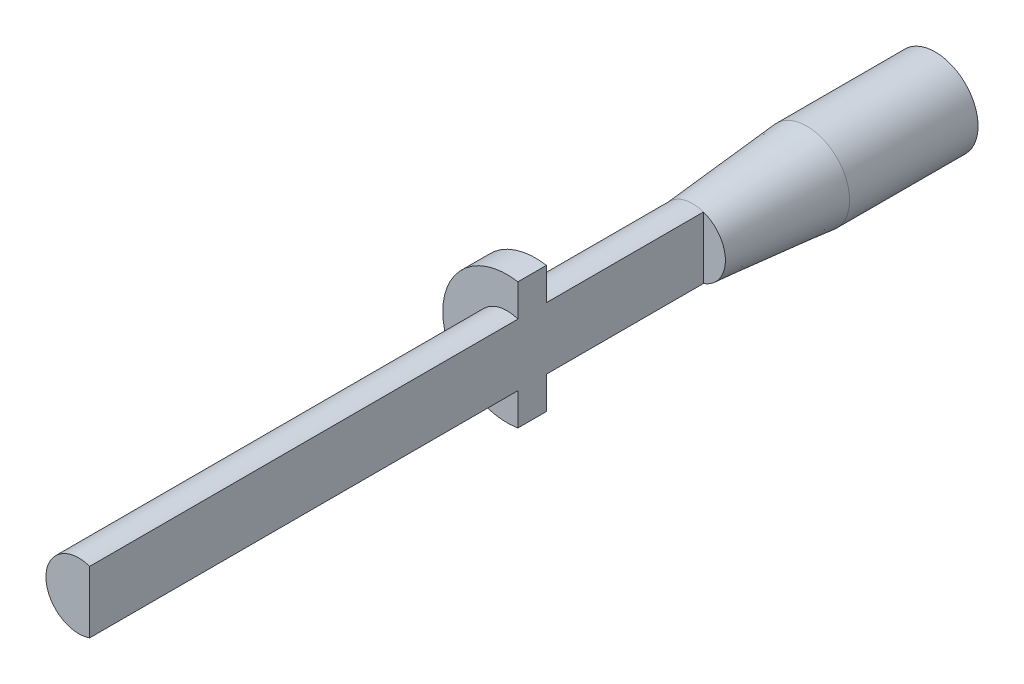
SolidWorks part; units mm, degrees
ref_plane "Front Plane" through (0, 0, 0) normal (0, 0, 1) x (1, 0, 0)
ref_plane "Top Plane" through (0, 0, 0) normal (0, 1, 0) x (1, 0, 0)
ref_plane "Right Plane" through (0, 0, 0) normal (1, 0, 0) x (0, 0, -1)
sketch "Sketch1" plane through (0, 0, 0) normal (0, 0, 1) x (1, 0, 0)
  line L0 (0.7623, -2.17) -> (0.7623, 2.17)
  arc A0 (0.7623, 2.17) -> (0.7623, -2.17) centre (0, 0) ccw
  dimension "D1" = 4.6
  dimension "D2" = 4.34
sketch "Sketch2" plane through (0, 0, 0) normal (0, 0, 1) x (1, 0, 0)
  line L0 (0.7623, -4.435) -> (0.7623, 4.435)
  arc A0 (0.7623, 4.435) -> (0.7623, -4.435) centre (0, 0) ccw
  dimension "D1" = 9
extrude "Boss-Extrude2" add sketch "Sketch2" against normal blind 2
extrude "Boss-Extrude3" add sketch "Sketch1" along normal blind 30 and the other way blind 30
sketch "Sketch3" plane through (0, 0, -30) normal (0, 0, -1) x (-1, 0, 0)
  circle A0 centre (0, 0) radius 3
  dimension "D1" = 6
extrude "Boss-Extrude4" add sketch "Sketch3" against normal blind 17
sketch "Sketch4" plane through (0, 0, -30) normal (0, 0, -1) x (-1, 0, 0)
  line L2 (-1.59, 1.4098) -> (-1.59, -1.4098)
  arc A1 (-1.59, -1.4098) -> (-1.59, 1.4098) centre (0, 0) ccw
  dimension "D1" = 1.59
  dimension "D3" = 4.25
extrude "Cut-Extrude1" cut sketch "Sketch4" against normal blind 7.5
sketch "Sketch7" plane through (0, 0, 0) normal (1, 0, 0) x (0, 0, -1)
  line L0 (13, 3) -> (21, 3)
  line L1 (30, 3) -> (13, 3) construction
  line L2 (21, 3) -> (13, 2.3)
  line L3 (13, 2.3) -> (13, 3)
  line L4 (-30.3622, 0) -> (46.5489, 0) construction
  point P13 (-30.3622, 0)
  dimension "D1" = 8
revolve "Cut-Revolve1" cut sketch "Sketch7" angle 360 about L4
